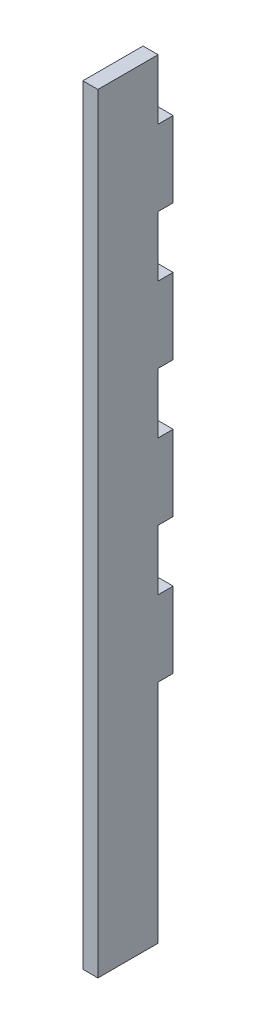
SolidWorks part; units mm, degrees
material "Acrylic (Medium-high impact)"
ref_plane "Front" through (0, 0, 0) normal (0, 0, 1) x (1, 0, 0)
ref_plane "Top" through (0, 0, 0) normal (0, 1, 0) x (1, 0, 0)
ref_plane "Right" through (0, 0, 0) normal (1, 0, 0) x (0, 0, -1)
sketch "Sketch1" plane through (0, 0, 0) normal (1, 0, 0) x (0, 0, -1)
  line L3 (-7.9375, -162.306) -> (7.9375, -162.306)
  line L69 (7.9375, 0) -> (7.9375, -162.306)
  line L70 (-7.9375, -162.306) -> (-7.9375, 0)
  line L71 (4.7625, -127.3048) -> (4.7625, -143.256)
  line L74 (6.35, -12.7) -> (6.35, -28.6512) construction
  line L75 (6.35, -41.3512) -> (6.35, -57.3024) construction
  line L76 (6.35, -70.0024) -> (6.35, -85.9536) construction
  line L77 (6.35, -98.6536) -> (6.35, -114.6048) construction
  line L82 (7.9375, 0) -> (-7.9375, 0)
  line L83 (7.9375, 0) -> (7.9375, -12.7)
  line L84 (7.9375, 0) -> (4.7625, 0)
  line L85 (4.7625, 0) -> (4.7625, -12.7)
  line L86 (7.9375, -12.7) -> (4.7625, -12.7)
  line L87 (7.9375, -28.6512) -> (7.9375, -41.3512)
  line L88 (7.9375, -28.6512) -> (4.7625, -28.6512)
  line L89 (4.7625, -28.6512) -> (4.7625, -41.3512)
  line L90 (7.9375, -41.3512) -> (4.7625, -41.3512)
  line L91 (7.9375, -57.3024) -> (7.9375, -70.0024)
  line L92 (7.9375, -57.3024) -> (4.7625, -57.3024)
  line L93 (4.7625, -57.3024) -> (4.7625, -70.0024)
  line L94 (7.9375, -70.0024) -> (4.7625, -70.0024)
  line L95 (7.9375, -85.9536) -> (7.9375, -98.6536)
  line L96 (7.9375, -85.9536) -> (4.7625, -85.9536)
  line L97 (4.7625, -85.9536) -> (4.7625, -98.6536)
  line L98 (7.9375, -98.6536) -> (4.7625, -98.6536)
  line L107 (6.35, -127.3048) -> (6.35, -143.256) construction
  line L108 (7.9375, -114.6048) -> (4.7625, -114.6048)
  line L109 (7.9375, -114.6048) -> (7.9375, -127.3048)
  line L110 (7.9375, -127.3048) -> (4.7625, -127.3048)
  line L111 (4.7625, -114.6048) -> (4.7625, -127.3048)
  line L113 (4.7625, -143.256) -> (7.9375, -143.256)
  line L114 (4.7625, -143.256) -> (4.7625, -155.956)
  line L115 (4.7625, -155.956) -> (7.9375, -155.956)
  line L116 (7.9375, -143.256) -> (7.9375, -155.956)
  line L117 (7.9375, -155.956) -> (4.7625, -155.956)
  line L118 (7.9375, -155.956) -> (7.9375, -162.306)
  line L119 (7.9375, -162.306) -> (4.7625, -162.306)
  line L120 (4.7625, -155.956) -> (4.7625, -162.306)
  point P4 (0, -162.306)
  point P44 (6.35, -143.256)
  dimension "D2" = 12.7
  dimension "D4" = 3.175
  dimension "D3" = 6.35
  dimension "D1" = 15.9512
  dimension "D5" = 12.7
extrude "Boss-Extrude1" add sketch "Sketch1" along normal blind 3.175 contours L120 L114 L71 L111 L108 L69 L98 L97 L96 L94 L93 L92 L90 L89 L88 L86 L85 L82 L70 L3
sketch "Sketch2" plane through (3.175, 0, 0) normal (1, 0, 0) x (0, 0, -1)
  line L6 (7.9375, -70.0024) -> (20.1295, -70.0024)
  line L7 (7.9375, -70.0024) -> (7.9375, -85.9536)
  line L8 (7.9375, -85.9536) -> (20.1295, -85.9536)
  line L9 (20.1295, -70.0024) -> (20.1295, -85.9536)
  line L11 (7.9375, -76.3905) -> (13.7795, -76.3905)
  line L12 (7.9375, -76.3905) -> (7.9375, -79.5655)
  line L13 (7.9375, -79.5655) -> (13.7795, -79.5655)
  line L14 (13.7795, -76.3905) -> (13.7795, -79.5655)
  line L31 (7.9375, -70.0024) -> (4.7625, -70.0024) construction
  point P22 (13.7795, -77.978)
  point P27 (20.1295, -77.978)
  dimension "D1" = 12.192
  dimension "D3" = 3.175
  dimension "D4" = 5.842
extrude "Boss-Extrude2" [suppressed] add sketch "Sketch2" against normal up to surface (2.9972 mm away)
equation "\"bottomThickness\"= .25in"
equation "\"wallThickness\"= .125in"
equation "\"D4@Sketch1\"=\"wallThickness\""
equation "\"D3@Sketch1\"=\"bottomThickness\""
equation "\"D1@Boss-Extrude1\"=\"wallThickness\""
